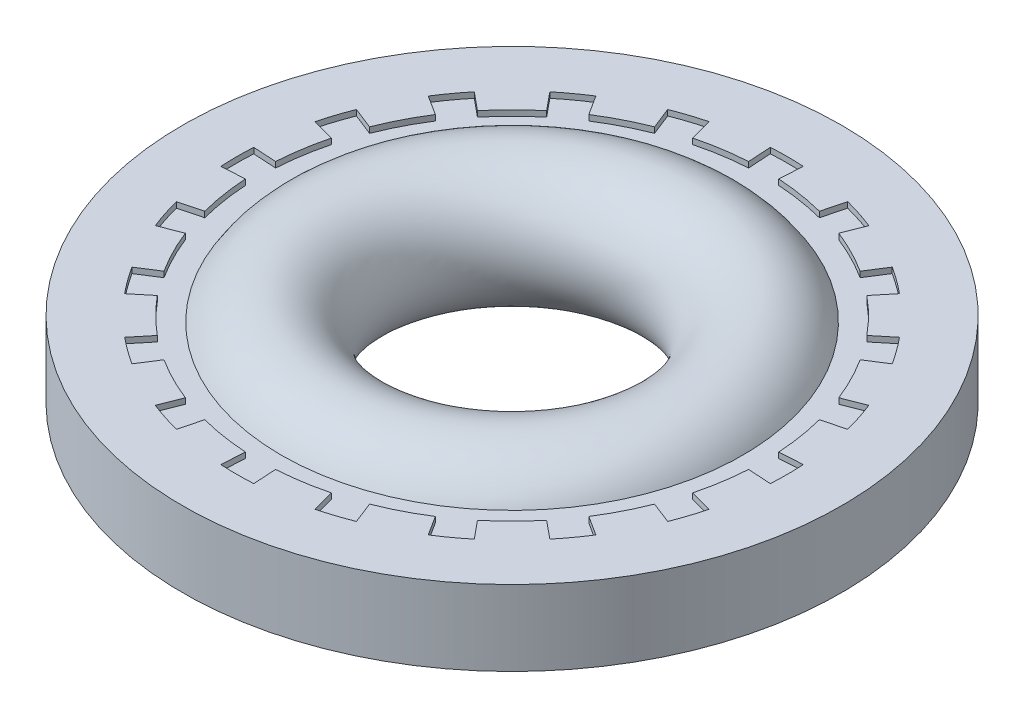
SolidWorks part; units mm, degrees
ref_plane "Front Plane" through (0, 0, 0) normal (0, 0, 1) x (1, 0, 0)
ref_plane "Top Plane" through (0, 0, 0) normal (0, 1, 0) x (1, 0, 0)
ref_plane "Right Plane" through (0, 0, 0) normal (1, 0, 0) x (0, 0, -1)
sketch "Sketch1" plane through (0, 0, 0) normal (0, 0, 1) x (1, 0, 0)
  line L0 (-4.8895, 0) -> (4.8895, 0) construction
  line L1 (0, 0) -> (0, 0.5588) construction
  line L3 (-4.8895, 0.5588) -> (-2.601, 0.5588)
  line L4 (-4.8895, 0.5588) -> (-4.8895, -0.5588)
  line L5 (-4.8895, -0.5588) -> (-2.601, -0.5588)
  line L6 (-2.601, 0.5588) -> (-2.601, -0.5588)
  circle A0 centre (-2.601, 0) radius 0.95
  point P3 (-1.651, 0)
  dimension "D1" = 1.8999
  dimension "D2" = 7.1018
sketch "Sketch2" plane through (0, 0, 0) normal (0, 0, 1) x (1, 0, 0)
  line L0 (-4.8895, 0.5588) -> (-4.8895, -0.5588) construction
  line L2 (-4.8895, 0.5588) -> (-2.601, 0.5588) construction
  line L3 (-4.8895, -0.5588) -> (-2.601, -0.5588) construction
  line L4 (-4.8895, 0.5588) -> (-4.8895, -0.5588)
  line L5 (-3.7391, 0.5588) -> (-3.7391, -0.5588)
  line L6 (-4.8895, 0.5588) -> (-3.7391, 0.5588)
  line L7 (-4.8895, -0.5588) -> (-3.7391, -0.5588)
  line L8 (0, 0) -> (0, 0.5588) construction
  line L9 (0, 0) -> (0, 0.5588) construction
  line L10 (-3.5509, 0.5588) -> (-3.5509, -0.5588) construction
  circle A0 centre (-2.601, 0) radius 0.95 construction
  dimension "D1" = 7.4782
revolve "Revolve1" add sketch "Sketch2" angle 360 about L9
sketch "Sketch3" plane through (0, 0.5588, 0) normal (0, 1, 0) x (1, 0, 0)
  line L0 (-0.2239, 3.7324) -> (-0.2445, 4.0762)
  line L1 (0.2239, 3.7324) -> (0.2445, 4.0762)
  circle A0 centre (0, 0) radius 4.0836 construction
  circle A1 centre (0, 0) radius 3.7391 construction
  arc A3 (0.2445, 4.0762) -> (-0.2445, 4.0762) centre (0, 0) ccw
  arc A4 (0.2239, 3.7324) -> (-0.2239, 3.7324) centre (0, 0) ccw
  dimension "D1" = 8.1671
  dimension "D2" = 0.4889
extrude "Cut-Extrude1" cut sketch "Sketch3" against normal through all
pattern_circular "CirPattern1" count 20 over 360 about axis through (0, 0, 0) along (0, 1, 0) of "Cut-Extrude1"
sketch "Sketch4" plane through (0, 0, 0) normal (0, 0, 1) x (1, 0, 0)
  line L3 (-4.0836, -0.475) -> (-3.4236, -0.475)
  line L4 (-4.0836, 0.475) -> (-3.4236, 0.475)
  line L5 (-4.0836, 0.475) -> (-4.0836, -0.475)
  line L6 (0, 0) -> (0, 0.5588) construction
  line L7 (0, 0) -> (0, 0.5588) construction
  circle A0 centre (-2.601, 0) radius 0.95 construction
  arc A1 (-3.4236, -0.475) -> (-3.4236, 0.475) centre (-2.601, 0) ccw
  dimension "D1" = 0.95
  dimension "D2" = 8.1671
revolve "Revolve2" add sketch "Sketch4" angle 360 about L7
sketch "Sketch5" plane through (0, 0, 0) normal (0, 1, 0) x (1, 0, 0)
  circle A0 centre (0, 0) radius 1.651
  circle A1 centre (0, 0) radius 4.8895 construction
  circle A2 centre (0, 0) radius 4.8895
equation "\"D1@Sketch1\" = \"thickness@Sketch1\"*1.7"
equation "\"D2@Sketch3\" = \"OD@Sketch1\"/20"
equation "\"D1@Sketch4\" = \"thickness@Sketch1\"*.85"
equation "\"D1@Sketch3\" = \"D2@Sketch1\"*1.15"
equation "\"D1@Sketch2\" = \"D2@Sketch1\"*1.053"
equation "\"D2@Sketch4\" = \"D1@Sketch3\""
